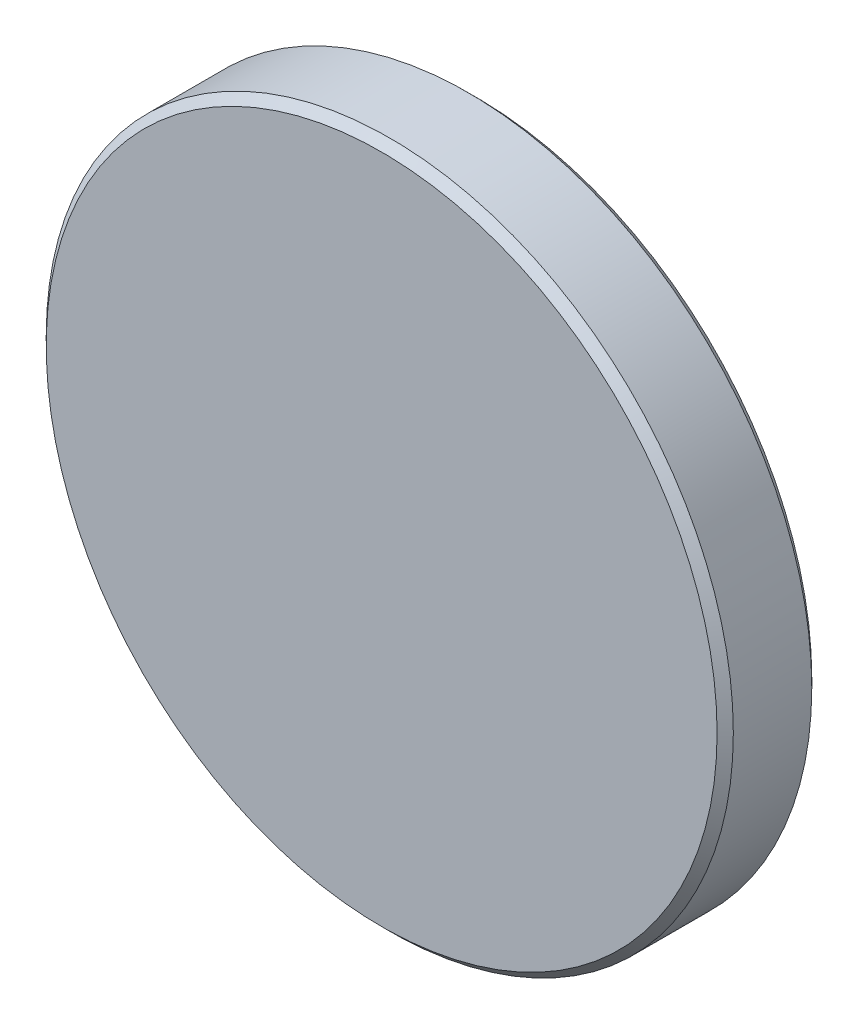
SolidWorks part; units mm, degrees
ref_plane "前视基准面" through (0, 0, 0) normal (0, 0, 1) x (1, 0, 0)
ref_plane "上视基准面" through (0, 0, 0) normal (0, 1, 0) x (1, 0, 0)
ref_plane "右视基准面" through (0, 0, 0) normal (1, 0, 0) x (0, 0, -1)
sketch "草图1" plane through (0, 0, 0) normal (0, 0, 1) x (1, 0, 0)
  circle A0 centre (0, 0) radius 12.7
  dimension "D1" = 25.4
extrude "凸台-拉伸1" add sketch "草图1" along normal blind 3.5
chamfer "倒角1" distance 0.3 angle 45 2 edges at (12.7, 0, 0) (12.7, 0, 3.5)
